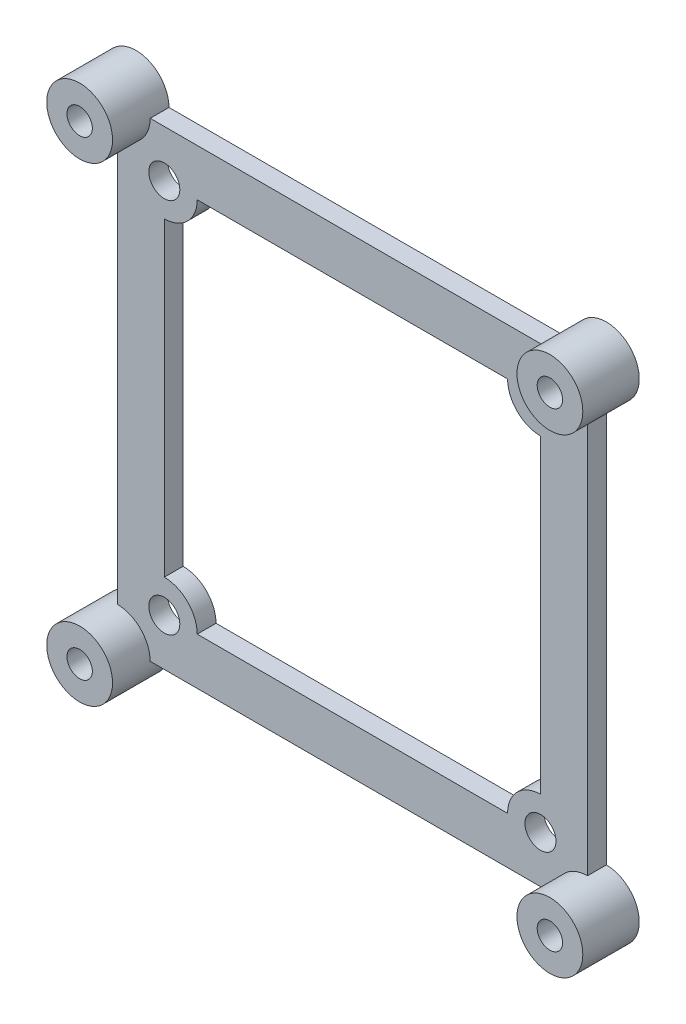
SolidWorks part; units mm, degrees
ref_plane "Front Plane" through (0, 0, 0) normal (0, 0, 1) x (1, 0, 0)
ref_plane "Top Plane" through (0, 0, 0) normal (0, 1, 0) x (1, 0, 0)
ref_plane "Right Plane" through (0, 0, 0) normal (1, 0, 0) x (0, 0, -1)
sketch "Sketch1" plane through (0, 0, 0) normal (0, 0, 1) x (1, 0, 0)
  line L0 (-16.5, 20) -> (16.5, 20)
  line L1 (20, 20) -> (-20, 20) construction
  line L2 (20, 20) -> (20, -20) construction
  line L3 (20, -20) -> (-20, -20) construction
  line L4 (-20, 20) -> (-20, -20) construction
  line L5 (20, 20) -> (-20, -20) construction
  line L6 (20, -20) -> (-20, 20) construction
  line L7 (25, 25) -> (-25, 25) construction
  line L8 (25, 25) -> (25, -25) construction
  line L9 (25, -25) -> (-25, -25) construction
  line L10 (-25, 25) -> (-25, -25) construction
  line L11 (25, 25) -> (-25, -25) construction
  line L12 (25, -25) -> (-25, 25) construction
  line L13 (-20, 16.5) -> (-20, -16.5)
  line L14 (-16.5, -20) -> (16.5, -20)
  line L15 (20, 16.5) -> (20, -16.5)
  line L16 (-21.5, 25) -> (21.5, 25)
  line L17 (25, 21.5) -> (25, -21.5)
  line L18 (-25, 21.5) -> (-25, -21.5)
  line L19 (-21.5, -25) -> (21.5, -25)
  circle A0 centre (-20, 20) radius 1.65
  circle A1 centre (-25, 25) radius 1.65
  circle A2 centre (20, 20) radius 1.65
  circle A3 centre (25, 25) radius 1.65
  circle A4 centre (25, -25) radius 1.65
  circle A5 centre (20, -20) radius 1.65
  circle A6 centre (-20, -20) radius 1.65
  circle A7 centre (-25, -25) radius 1.65
  arc A8 (-21.5, 25) -> (-25, 21.5) centre (-25, 25) ccw
  arc A9 (-20, 16.5) -> (-16.5, 20) centre (-20, 20) ccw
  arc A10 (16.5, 20) -> (20, 16.5) centre (20, 20) ccw
  arc A11 (25, 21.5) -> (21.5, 25) centre (25, 25) ccw
  arc A12 (21.5, -25) -> (25, -21.5) centre (25, -25) ccw
  arc A13 (20, -16.5) -> (16.5, -20) centre (20, -20) ccw
  arc A14 (-16.5, -20) -> (-20, -16.5) centre (-20, -20) ccw
  arc A15 (-25, -21.5) -> (-21.5, -25) centre (-25, -25) ccw
  point P0 (0, 0)
  point P6 (0, 0)
  dimension "D5" = 3.3
  dimension "D6" = 7
  dimension "D1" = 50
  dimension "D2" = 50
  dimension "D3" = 40
  dimension "D4" = 40
extrude "Boss-Extrude1" add sketch "Sketch1" along normal blind 2
sketch "Sketch2" plane through (0, 0, 2) normal (0, 0, 1) x (1, 0, 0)
  circle A0 centre (-25, 25) radius 1.65
  circle A1 centre (-25, 25) radius 3.5
  circle A2 centre (25, 25) radius 1.5707
  circle A3 centre (25, 25) radius 3.5
  circle A4 centre (-25, -25) radius 1.65
  circle A5 centre (-25, -25) radius 3.5
  circle A6 centre (25, -25) radius 1.65
  circle A7 centre (25, -25) radius 3.5
extrude "Boss-Extrude2" add sketch "Sketch2" along normal blind 4
sketch "Sketch3" plane through (0, 0, 6) normal (0, 0, 1) x (1, 0, 0)
  circle A17 centre (-25, 25) radius 1.35
  circle A18 centre (25, 25) radius 1.35
  circle A19 centre (25, -25) radius 1.35
  circle A20 centre (-25, -25) radius 1.35
  dimension "D1" = 2.7
extrude "Extrude-Thin1" add sketch "Sketch3" against normal up to surface (6 mm away) thin
